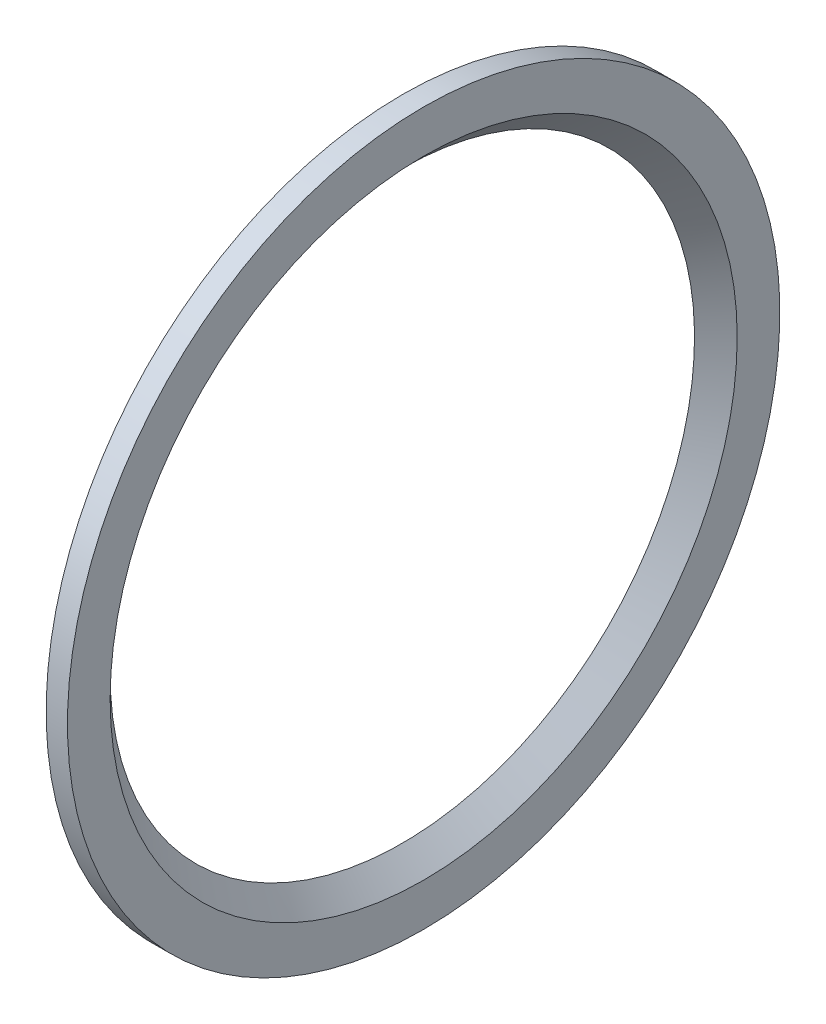
SolidWorks part; units mm, degrees
material "5052-H32"
ref_plane "Přední rovina" through (0, 0, 0) normal (0, 0, 1) x (1, 0, 0)
ref_plane "Horní rovina" through (0, 0, 0) normal (0, 1, 0) x (1, 0, 0)
ref_plane "Pravá rovina" through (0, 0, 0) normal (1, 0, 0) x (0, 0, -1)
sketch "Skica1" plane through (0, 0, 0) normal (0, 0, 1) x (1, 0, 0)
  line L0 (-115.05, -33.4) -> (-117.05, -33.4) construction
  line L1 (-115.05, -33.4) -> (-115.05, -29.4) construction
  line L2 (-117.05, -27.4) -> (-115.05, -29.4) construction
  line L3 (-117.05, -33.4) -> (-117.05, -27.4) construction
  line L4 (-115.05, -33.4) -> (-117.05, -33.4)
  line L5 (-115.05, -33.4) -> (-115.05, -29.4)
  line L6 (-117.05, -27.4) -> (-115.05, -29.4)
  line L7 (-117.05, -33.4) -> (-117.05, -27.4)
  line L8 (-67.4823, 0) -> (-363.0393, 0) construction
  line L9 (-67.4823, 0) -> (-363.0393, 0) construction
revolve "Rotovat1" add sketch "Skica1" angle 360 about L9
